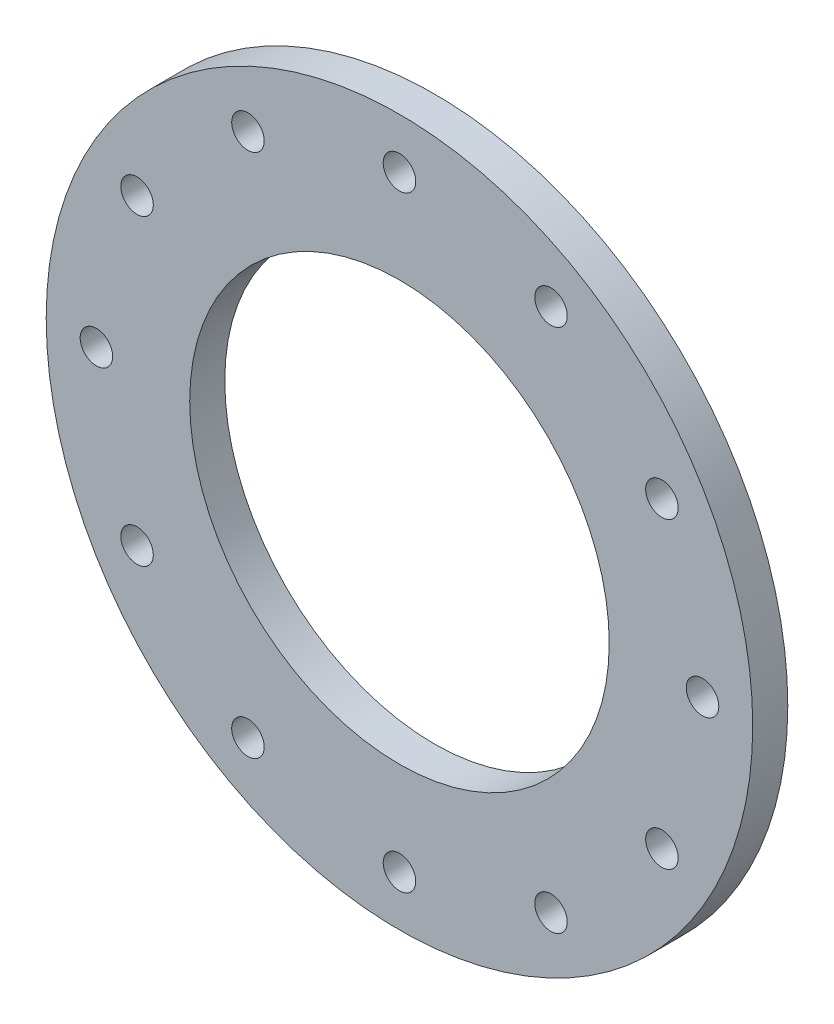
SolidWorks part; units mm, degrees
ref_plane "Front Plane" through (0, 0, 0) normal (0, 0, 1) x (1, 0, 0)
ref_plane "Top Plane" through (0, 0, 0) normal (0, 1, 0) x (1, 0, 0)
ref_plane "Right Plane" through (0, 0, 0) normal (1, 0, 0) x (0, 0, -1)
sketch "Sketch1" plane through (0, 0, 0.2) normal (0, 0, 1) x (1, 0, 0)
  circle A2 centre (-17.5, -28.25) radius 32
  circle A3 centre (-17.5, -55.7) radius 1.1303 construction
  circle A4 centre (-17.5, -55.7) radius 1.1303 construction
  circle A5 centre (-17.5, -55.7) radius 1.4732
  circle A6 centre (-31.225, -52.0224) radius 1.4732
  circle A7 centre (-41.2724, -41.975) radius 1.4732
  circle A8 centre (-44.95, -28.25) radius 1.4732
  circle A9 centre (-41.2724, -14.525) radius 1.4732
  circle A10 centre (-31.225, -4.4776) radius 1.4732
  circle A11 centre (-17.5, -0.8) radius 1.4732
  circle A12 centre (-3.775, -4.4776) radius 1.4732
  circle A13 centre (6.2724, -14.525) radius 1.4732
  circle A14 centre (9.95, -28.25) radius 1.4732
  circle A15 centre (6.2724, -41.975) radius 1.4732
  circle A16 centre (-3.775, -52.0224) radius 1.4732
  circle A17 centre (-17.5, -28.25) radius 19
  point P33 (-17.5, -28.25)
  dimension "D1" = 64
  dimension "D2" = 2.9464
  dimension "D4" = 38
  dimension "D3" = 12
extrude "Boss-Extrude1" add sketch "Sketch1" along normal blind 3.175
